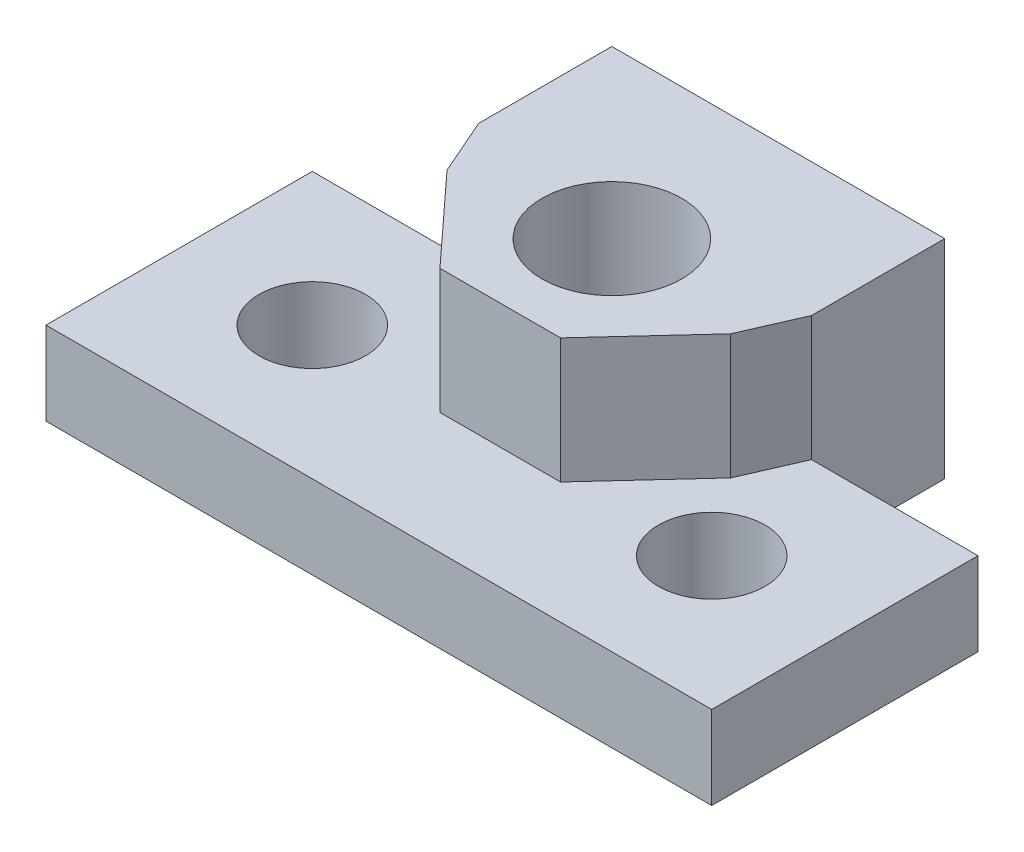
SolidWorks part; units mm, degrees
ref_plane "Front Plane" through (0, 0, 0) normal (0, 0, 1) x (1, 0, 0)
ref_plane "Top Plane" through (0, 0, 0) normal (0, 1, 0) x (1, 0, 0)
ref_plane "Right Plane" through (0, 0, 0) normal (1, 0, 0) x (0, 0, -1)
sketch "Sketch1" plane through (0, 0, 0) normal (0, 1, 0) x (1, 0, 0)
  line L0 (-5, -1.6667) -> (-10, -1.6667)
  line L1 (-10, -1.6667) -> (-10, -9.6667)
  line L2 (-10, -9.6667) -> (10, -9.6667)
  line L3 (10, -9.6667) -> (10, -1.6667)
  line L4 (10, -1.6667) -> (5, -1.6667)
  line L5 (5, -1.6667) -> (5, 2.3333)
  line L6 (5, 2.3333) -> (-5, 2.3333)
  line L7 (-5, -1.6667) -> (-5, 2.3333)
  circle A0 centre (-6, -5.6667) radius 1.6
  circle A1 centre (6, -5.6667) radius 1.6
  circle A2 centre (0, -2.6667) radius 2.5
  point P14 (0, -9.6667)
  point P16 (0, 2.3333)
  dimension "D1" = 3.2
  dimension "D9" = 5
  dimension "D2" = 4
  dimension "D3" = 4
  dimension "D4" = 4
  dimension "D5" = 4
  dimension "D6" = 4
  dimension "D7" = 4
  dimension "D8" = 12
  dimension "D10" = 3
  dimension "D11" = 5
  dimension "D12" = 5
extrude "Boss-Extrude1" add sketch "Sketch1" along normal mid plane 2.5
sketch "Sketch2" plane through (0, 0, 0) normal (0, 1, 0) x (1, 0, 0)
  line L0 (-5, 2.3333) -> (-5, -1.6667)
  line L1 (-5, -1.6667) -> (-4.2608, -3.3578)
  line L2 (-4.2608, -3.3578) -> (-1.8108, -6.0207)
  line L3 (-1.8108, -6.0207) -> (1.8108, -6.0207)
  line L4 (-5, 2.3333) -> (5, 2.3333)
  line L5 (5, 2.3333) -> (-5, 2.3333) construction
  line L6 (0, -6.0207) -> (0, 2.3333) construction
  line L7 (4.2608, -3.3578) -> (1.8108, -6.0207)
  line L8 (5, -1.6667) -> (4.2608, -3.3578)
  line L9 (5, 2.3333) -> (5, -1.6667)
  circle A0 centre (0, -2.6667) radius 2.5 construction
  circle A1 centre (0, -2.6667) radius 2.1
  point P14 (0, -0.1667)
  point P15 (2.5, -2.6667)
extrude "Boss-Extrude2" add sketch "Sketch2" along normal blind 5
equation "\"pading\"=4"
equation "\"D2@Sketch1\"=\"pading\""
equation "\"D3@Sketch1\"=\"pading\""
equation "\"D4@Sketch1\"=\"pading\""
equation "\"D5@Sketch1\"=\"pading\""
equation "\"D6@Sketch1\"=\"pading\""
equation "\"D7@Sketch1\"=\"pading\""
